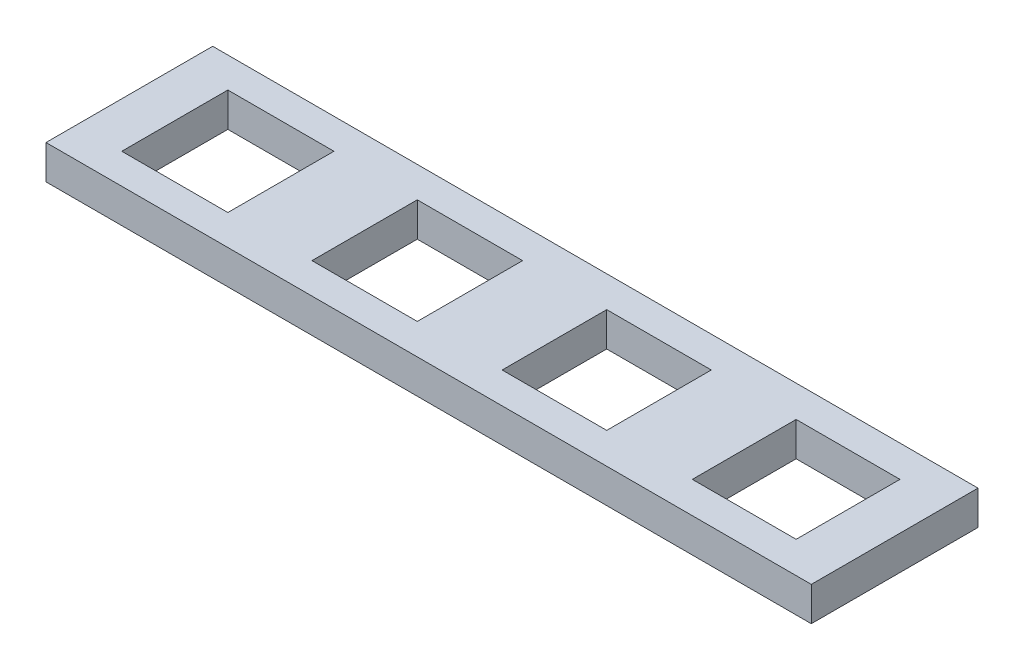
SolidWorks part; units mm, degrees
ref_plane "Front Plane" through (0, 0, 0) normal (0, 0, 1) x (1, 0, 0)
ref_plane "Top Plane" through (0, 0, 0) normal (0, 1, 0) x (1, 0, 0)
ref_plane "Right Plane" through (0, 0, 0) normal (1, 0, 0) x (0, 0, -1)
sketch "Sketch2" [suppressed] plane through (0, 0, 0) normal (0, 1, 0) x (1, 0, 0)
  line L0 (70, 25) -> (70, 0) construction
  line L1 (0, 0) -> (140, 0)
  line L2 (0, 0) -> (0, 25)
  line L3 (0, 25) -> (140, 25)
  line L4 (140, 0) -> (140, 25)
  line L5 (62.25, 20.25) -> (77.75, 20.25)
  line L6 (62.25, 20.25) -> (62.25, 4.75)
  line L7 (62.25, 4.75) -> (77.75, 4.75)
  line L8 (77.75, 20.25) -> (77.75, 4.75)
  line L9 (62.25, 20.25) -> (77.75, 4.75) construction
  line L10 (62.25, 4.75) -> (77.75, 20.25) construction
  line L11 (0, 12.5) -> (140, 12.5) construction
  line L12 (87.25, 20.25) -> (87.25, 4.75) construction
  line L13 (87.25, 20.25) -> (102.75, 20.25) construction
  line L14 (102.75, 20.25) -> (102.75, 4.75) construction
  line L15 (87.25, 4.75) -> (102.75, 4.75) construction
  line L16 (112.25, 20.25) -> (112.25, 4.75) construction
  line L17 (112.25, 20.25) -> (127.75, 20.25) construction
  line L18 (127.75, 20.25) -> (127.75, 4.75) construction
  line L19 (112.25, 4.75) -> (127.75, 4.75) construction
  line L20 (62.25, 20.25) -> (62.25, 4.75)
  line L21 (62.25, 20.25) -> (77.75, 20.25)
  line L22 (77.75, 20.25) -> (77.75, 4.75)
  line L23 (62.25, 4.75) -> (77.75, 4.75)
  line L24 (87.25, 20.25) -> (87.25, 4.75) construction
  line L25 (87.25, 20.25) -> (102.75, 20.25) construction
  line L26 (102.75, 20.25) -> (102.75, 4.75) construction
  line L27 (87.25, 4.75) -> (102.75, 4.75) construction
  line L28 (37.25, 20.25) -> (37.25, 4.75) construction
  line L29 (37.25, 20.25) -> (52.75, 20.25) construction
  line L30 (52.75, 20.25) -> (52.75, 4.75) construction
  line L31 (37.25, 4.75) -> (52.75, 4.75) construction
  line L32 (62.25, 20.25) -> (62.25, 4.75)
  line L33 (62.25, 20.25) -> (77.75, 20.25)
  line L34 (77.75, 20.25) -> (77.75, 4.75)
  line L35 (62.25, 4.75) -> (77.75, 4.75)
  line L36 (37.25, 20.25) -> (37.25, 4.75) construction
  line L37 (37.25, 20.25) -> (52.75, 20.25) construction
  line L38 (52.75, 20.25) -> (52.75, 4.75) construction
  line L39 (37.25, 4.75) -> (52.75, 4.75) construction
  line L40 (12.25, 20.25) -> (12.25, 4.75) construction
  line L41 (12.25, 20.25) -> (27.75, 20.25) construction
  line L42 (27.75, 20.25) -> (27.75, 4.75) construction
  line L43 (12.25, 4.75) -> (27.75, 4.75) construction
  line L44 (37.75, 19.75) -> (52.25, 19.75)
  line L45 (52.25, 19.75) -> (52.25, 5.25)
  line L46 (37.75, 5.25) -> (52.25, 5.25)
  line L47 (37.75, 19.75) -> (37.75, 5.25)
  line L48 (13.25, 19.25) -> (26.75, 19.25)
  line L49 (26.75, 19.25) -> (26.75, 5.75)
  line L50 (13.25, 5.75) -> (26.75, 5.75)
  line L51 (13.25, 19.25) -> (13.25, 5.75)
  line L52 (86.75, 20.75) -> (103.25, 20.75)
  line L53 (103.25, 20.75) -> (103.25, 4.25)
  line L54 (86.75, 4.25) -> (103.25, 4.25)
  line L55 (86.75, 20.75) -> (86.75, 4.25)
  line L56 (111.25, 21.25) -> (128.75, 21.25)
  line L57 (128.75, 21.25) -> (128.75, 3.75)
  line L58 (111.25, 3.75) -> (128.75, 3.75)
  line L59 (111.25, 21.25) -> (111.25, 3.75)
  point P5 (70, 12.5)
  dimension "D1" = 140
  dimension "D2" = 25
  dimension "D3" = 15.5
  dimension "D4" = 15.5
  dimension "D5" = 3
  dimension "D6" = 3
  dimension "D7" = 0.5
  dimension "D8" = 1
  dimension "D9" = 0.5
  dimension "D10" = 1
extrude "Boss-Extrude4" [suppressed] add sketch "Sketch2" along normal blind 5 contours L2 L1 L4 L3 | L48 L49 L50 L51 | L44 L45 L46 L47 | L52 L53 L54 L55 | L56 L57 L58 L59 | L20 L23 L22 L21
sketch "Sketch3" plane through (0, 0, 0) normal (0, 1, 0) x (1, 0, 0)
  line L0 (13, 18) -> (13, 4) construction
  line L9 (0, 0) -> (101, 0)
  line L10 (0, 0) -> (0, 22)
  line L11 (0, 22) -> (101, 22)
  line L12 (101, 0) -> (101, 22)
  line L13 (6, 18) -> (20, 18)
  line L14 (6, 18) -> (6, 4)
  line L15 (6, 4) -> (20, 4)
  line L16 (20, 18) -> (20, 4)
  line L21 (38, 18) -> (38, 4) construction
  line L26 (63, 18) -> (63, 4) construction
  line L27 (31, 18) -> (45, 18) construction
  line L28 (45, 18) -> (45, 4) construction
  line L29 (31, 4) -> (45, 4) construction
  line L30 (31, 18) -> (31, 4) construction
  line L31 (56, 18) -> (70, 18) construction
  line L32 (70, 18) -> (70, 4) construction
  line L33 (56, 4) -> (70, 4) construction
  line L34 (56, 18) -> (56, 4) construction
  line L36 (31.05, 4.05) -> (44.95, 4.05)
  line L37 (31.05, 4.05) -> (31.05, 17.95)
  line L38 (31.05, 17.95) -> (44.95, 17.95)
  line L39 (44.95, 4.05) -> (44.95, 17.95)
  line L40 (31.05, 4.05) -> (44.95, 17.95) construction
  line L41 (31.05, 17.95) -> (44.95, 4.05) construction
  line L42 (56.1, 4.1) -> (69.9, 4.1)
  line L43 (56.1, 4.1) -> (56.1, 17.9)
  line L44 (56.1, 17.9) -> (69.9, 17.9)
  line L45 (69.9, 4.1) -> (69.9, 17.9)
  line L46 (56.1, 4.1) -> (69.9, 17.9) construction
  line L47 (56.1, 17.9) -> (69.9, 4.1) construction
  line L51 (88, 18) -> (88, 4) construction
  line L52 (81, 18) -> (95, 18)
  line L53 (95, 18) -> (95, 4)
  line L54 (81, 4) -> (95, 4)
  line L55 (81, 18) -> (81, 4)
  line L57 (81.15, 4.15) -> (94.85, 4.15)
  line L58 (81.15, 4.15) -> (81.15, 17.85)
  line L59 (81.15, 17.85) -> (94.85, 17.85)
  line L60 (94.85, 4.15) -> (94.85, 17.85)
  line L61 (81.15, 4.15) -> (94.85, 17.85) construction
  line L62 (81.15, 17.85) -> (94.85, 4.15) construction
  point P10 (13, 11)
  point P11 (38, 11)
  point P12 (63, 11)
  point P13 (38, 11)
  point P21 (63, 11)
  point P44 (88, 11)
  dimension "D1" = 101
  dimension "D2" = 22
  dimension "D3" = 14
  dimension "D4" = 13
  dimension "D5" = 11
  dimension "D7" = 25
  dimension "D8" = 25
  dimension "14.1" = 13.9
  dimension "D10" = 13.8
  dimension "D11" = 13.7
  dimension "D6" = 4
extrude "Boss-Extrude5" add sketch "Sketch3" along normal blind 4.5
